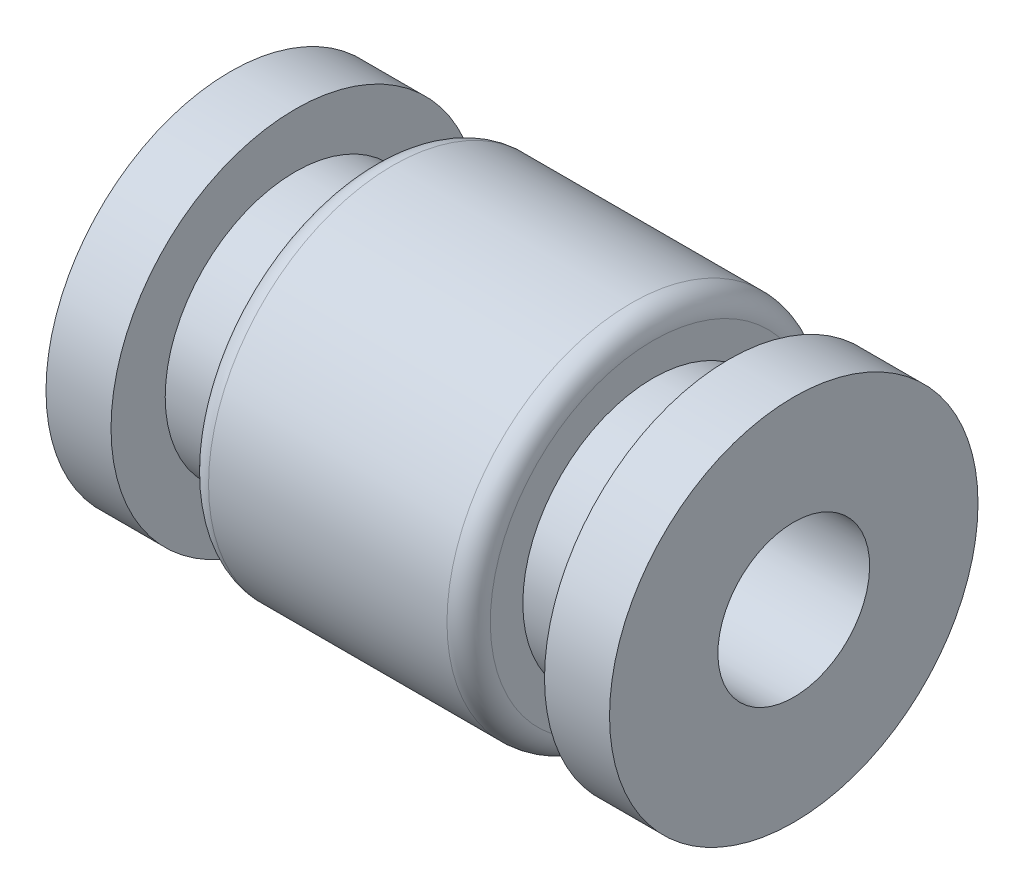
SolidWorks part; units mm, degrees
material "Silicon"
ref_plane "Front Plane" through (0, 0, 0) normal (0, 0, 1) x (1, 0, 0)
ref_plane "Top Plane" through (0, 0, 0) normal (0, 1, 0) x (1, 0, 0)
ref_plane "Right Plane" through (0, 0, 0) normal (1, 0, 0) x (0, 0, -1)
sketch "Sketch1" plane through (0, 0, 0) normal (0, 0, 1) x (1, 0, 0)
  line L0 (-6.5, 0) -> (-6.5, 4.25)
  line L1 (-6.5, 4.25) -> (-5, 4.25)
  line L2 (-5, 4.25) -> (-5, 3)
  line L3 (-5, 3) -> (-3.25, 3)
  line L4 (-3.25, 3) -> (-3.25, 4.25)
  line L5 (-3.25, 4.25) -> (3.25, 4.25)
  line L6 (3.25, 4.25) -> (3.25, 3)
  line L7 (3.25, 3) -> (5, 3)
  line L8 (5, 3) -> (5, 4.25)
  line L9 (5, 4.25) -> (6.5, 4.25)
  line L10 (6.5, 4.25) -> (6.5, 0)
  line L11 (6.5, 0) -> (-6.5, 0)
  line L12 (0, 0) -> (0, -8245.7939) construction
  dimension "D1" = 13
  dimension "D2" = 1.5
  dimension "D3" = 6.5
  dimension "D4" = 4.25
  dimension "D5" = 3
revolve "Revolve1" add sketch "Sketch1" angle 360 about L11
sketch "Sketch2" plane through (6.5, 0, 0) normal (1, 0, 0) x (0, 0, -1)
  circle A0 centre (0, 0) radius 1.75
  dimension "D1" = 3.5
extrude "Cut-Extrude1" cut sketch "Sketch2" against normal through all
fillet "Fillet1" radius 0.5 2 edges at (-3.25, 4.25, 0) (3.25, 4.25, 0)
